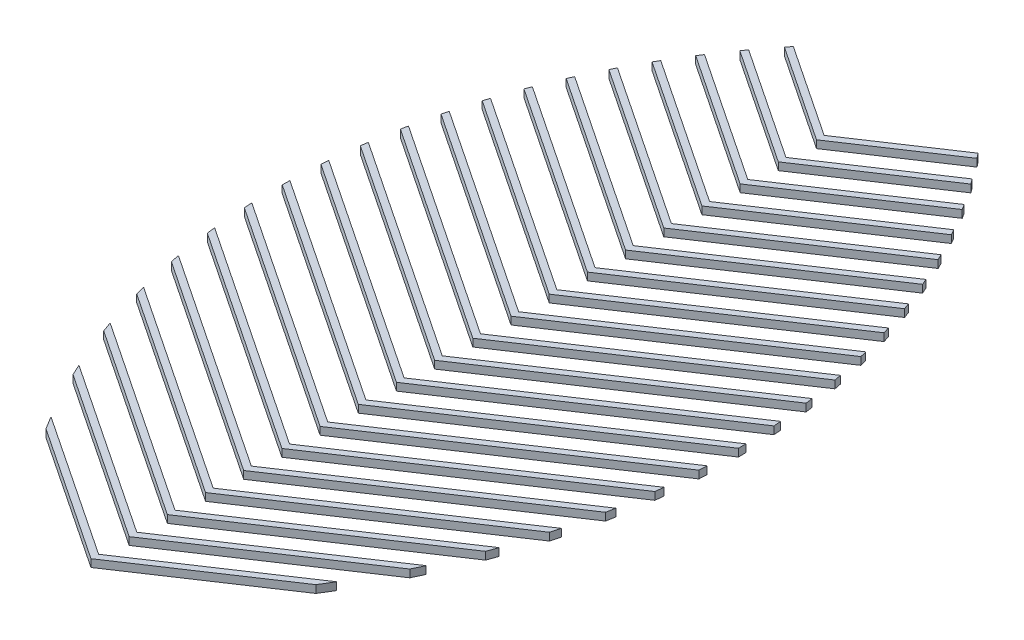
SolidWorks part; units mm, degrees
ref_plane "Front Plane" through (0, 0, 0) normal (0, 0, 1) x (1, 0, 0)
ref_plane "Top Plane" through (0, 0, 0) normal (0, 1, 0) x (1, 0, 0)
ref_plane "Right Plane" through (0, 0, 0) normal (1, 0, 0) x (0, 0, -1)
sketch "Sketch2" plane through (0, 0, 0) normal (0, 1, 0) x (1, 0, 0)
  line L0 (-15.0876, 6.8922) -> (8.6636, -8.942)
  line L1 (8.6636, -8.942) -> (32.4148, 6.8922)
  line L2 (-20.2008, 16.651) -> (8.6636, -2.592)
  line L3 (8.6636, -3.862) -> (8.6636, -8.942) construction
  line L4 (-13.7712, 4.7445) -> (8.6636, -10.212)
  line L5 (8.6636, -10.212) -> (31.0984, 4.7445)
  line L7 (8.6636, -8.942) -> (8.6636, -10.212) construction
  line L9 (8.6636, -2.592) -> (37.5281, 16.651)
  line L10 (-19.336, 14.8045) -> (8.6636, -3.862)
  line L11 (8.6636, -3.862) -> (36.6632, 14.8045)
  line L14 (8.6636, 2.488) -> (8.6636, -2.592) construction
  line L15 (8.6636, -2.592) -> (8.6636, -3.862) construction
  line L16 (-23.6775, 25.3188) -> (8.6636, 3.758)
  line L17 (8.6636, 3.758) -> (41.0047, 25.3188)
  line L18 (-23.0802, 23.6506) -> (8.6636, 2.488)
  line L19 (8.6636, 2.488) -> (40.4074, 23.6506)
  line L22 (8.6636, 8.838) -> (8.6636, 3.758) construction
  line L23 (8.6636, 3.758) -> (8.6636, 2.488) construction
  line L24 (-26.0837, 33.2729) -> (8.6636, 10.108)
  line L25 (8.6636, 10.108) -> (43.4109, 33.2729)
  line L26 (-25.6722, 31.7286) -> (8.6636, 8.838)
  line L27 (8.6636, 8.838) -> (42.9994, 31.7286)
  line L30 (8.6636, 15.188) -> (8.6636, 10.108) construction
  line L31 (8.6636, 10.108) -> (8.6636, 8.838) construction
  line L32 (-27.7036, 40.7028) -> (8.6636, 16.458)
  line L33 (8.6636, 16.458) -> (45.0308, 40.7028)
  line L34 (-27.4334, 39.2527) -> (8.6636, 15.188)
  line L35 (8.6636, 15.188) -> (44.7606, 39.2527)
  line L38 (8.6636, 21.538) -> (8.6636, 16.458) construction
  line L39 (8.6636, 16.458) -> (8.6636, 15.188) construction
  line L40 (-28.7043, 47.72) -> (8.6636, 22.808)
  line L41 (8.6636, 22.808) -> (46.0315, 47.72)
  line L42 (-28.5479, 46.3457) -> (8.6636, 21.538)
  line L43 (8.6636, 21.538) -> (45.8752, 46.3457)
  line L46 (8.6636, 27.888) -> (8.6636, 22.808) construction
  line L47 (8.6636, 22.808) -> (8.6636, 21.538) construction
  line L48 (-29.1937, 54.3963) -> (8.6636, 29.158)
  line L49 (8.6636, 29.158) -> (46.5209, 54.3963)
  line L50 (-29.1328, 53.0857) -> (8.6636, 27.888)
  line L51 (8.6636, 27.888) -> (46.4601, 53.0857)
  line L54 (8.6636, 34.238) -> (8.6636, 29.158) construction
  line L55 (8.6636, 29.158) -> (8.6636, 27.888) construction
  line L56 (-29.246, 60.7811) -> (8.6636, 35.508)
  line L57 (8.6636, 35.508) -> (46.5732, 60.7811)
  line L58 (-29.2677, 59.5256) -> (8.6636, 34.238)
  line L59 (8.6636, 34.238) -> (46.5949, 59.5256)
  line L62 (8.6636, 40.588) -> (8.6636, 35.508) construction
  line L63 (8.6636, 35.508) -> (8.6636, 34.238) construction
  line L64 (-28.9145, 66.9101) -> (8.6636, 41.858)
  line L65 (8.6636, 41.858) -> (46.2417, 66.9101)
  line L66 (-29.0094, 65.7034) -> (8.6636, 40.588)
  line L67 (8.6636, 40.588) -> (46.3367, 65.7034)
  line L70 (8.6636, 46.938) -> (8.6636, 41.858) construction
  line L71 (8.6636, 41.858) -> (8.6636, 40.588) construction
  line L72 (-28.2388, 72.8096) -> (8.6636, 48.208)
  line L73 (8.6636, 48.208) -> (45.566, 72.8096)
  line L74 (-28.3999, 71.647) -> (8.6636, 46.938)
  line L75 (8.6636, 46.938) -> (45.7271, 71.647)
  line L78 (8.6636, 53.288) -> (8.6636, 48.208) construction
  line L79 (8.6636, 48.208) -> (8.6636, 46.938) construction
  line L80 (-27.2489, 78.4997) -> (8.6636, 54.558)
  line L81 (8.6636, 54.558) -> (44.5761, 78.4997)
  line L82 (-27.4708, 77.3777) -> (8.6636, 53.288)
  line L83 (8.6636, 53.288) -> (44.798, 77.3777)
  line L86 (8.6636, 59.638) -> (8.6636, 54.558) construction
  line L87 (8.6636, 54.558) -> (8.6636, 53.288) construction
  line L88 (-25.968, 83.9958) -> (8.6636, 60.908)
  line L89 (8.6636, 60.908) -> (43.2952, 83.9958)
  line L90 (-26.2465, 82.9115) -> (8.6636, 59.638)
  line L91 (8.6636, 59.638) -> (43.5737, 82.9115)
  line L94 (8.6636, 65.988) -> (8.6636, 60.908) construction
  line L95 (8.6636, 60.908) -> (8.6636, 59.638) construction
  line L96 (-24.4139, 89.3097) -> (8.6636, 67.258)
  line L97 (8.6636, 67.258) -> (41.7411, 89.3097)
  line L98 (-24.7458, 88.261) -> (8.6636, 65.988)
  line L99 (8.6636, 65.988) -> (42.073, 88.261)
  line L102 (8.6636, 72.338) -> (8.6636, 67.258) construction
  line L103 (8.6636, 67.258) -> (8.6636, 65.988) construction
  line L104 (-22.6004, 94.4507) -> (8.6636, 73.608)
  line L105 (8.6636, 73.608) -> (39.9276, 94.4507)
  line L106 (-22.9833, 93.436) -> (8.6636, 72.338)
  line L107 (8.6636, 72.338) -> (40.3105, 93.436)
  line L110 (8.6636, 78.688) -> (8.6636, 73.608) construction
  line L111 (8.6636, 73.608) -> (8.6636, 72.338) construction
  line L112 (-20.5381, 99.4258) -> (8.6636, 79.958)
  line L113 (8.6636, 79.958) -> (37.8653, 99.4258)
  line L114 (-20.9701, 98.4438) -> (8.6636, 78.688)
  line L115 (8.6636, 78.688) -> (38.2973, 98.4438)
  line L118 (8.6636, 85.038) -> (8.6636, 79.958) construction
  line L119 (8.6636, 79.958) -> (8.6636, 78.688) construction
  line L120 (-18.2347, 104.2403) -> (8.6636, 86.308)
  line L121 (8.6636, 86.308) -> (35.562, 104.2403)
  line L122 (-18.7144, 103.29) -> (8.6636, 85.038)
  line L123 (8.6636, 85.038) -> (36.0416, 103.29)
  line L126 (8.6636, 91.388) -> (8.6636, 86.308) construction
  line L127 (8.6636, 86.308) -> (8.6636, 85.038) construction
  line L128 (-15.6958, 108.8976) -> (8.6636, 92.658)
  line L129 (8.6636, 92.658) -> (33.023, 108.8976)
  line L130 (-16.2222, 107.9786) -> (8.6636, 91.388)
  line L131 (8.6636, 91.388) -> (33.5494, 107.9786)
  line L134 (8.6636, 97.738) -> (8.6636, 92.658) construction
  line L135 (8.6636, 92.658) -> (8.6636, 91.388) construction
  line L136 (-12.9245, 113.4001) -> (8.6636, 99.008)
  line L137 (8.6636, 99.008) -> (30.2517, 113.4001)
  line L138 (-13.4973, 112.512) -> (8.6636, 97.738)
  line L139 (8.6636, 97.738) -> (30.8245, 112.512)
  line L142 (8.6636, 104.088) -> (8.6636, 99.008) construction
  line L143 (8.6636, 99.008) -> (8.6636, 97.738) construction
  line L144 (-9.9223, 117.7486) -> (8.6636, 105.358)
  line L145 (8.6636, 105.358) -> (27.2495, 117.7486)
  line L146 (-10.5412, 116.8912) -> (8.6636, 104.088)
  line L147 (8.6636, 104.088) -> (27.8684, 116.8912)
  line L150 (8.6636, 110.438) -> (8.6636, 105.358) construction
  line L151 (8.6636, 105.358) -> (8.6636, 104.088) construction
  line L152 (-6.6885, 121.9428) -> (8.6636, 111.708)
  line L153 (8.6636, 111.708) -> (24.0157, 121.9428)
  line L154 (-7.3538, 121.1163) -> (8.6636, 110.438)
  line L155 (8.6636, 110.438) -> (24.6811, 121.1163)
  line L158 (8.6636, 116.788) -> (8.6636, 111.708) construction
  line L159 (8.6636, 111.708) -> (8.6636, 110.438) construction
  arc A0 (-6.6885, 121.9428) -> (-7.3538, 121.1163) centre (71.3713, 58.4122) ccw
  arc A1 (24.0157, 121.9428) -> (24.6811, 121.1163) centre (-54.0441, 58.4122) cw
  arc A2 (32.4148, 6.8922) -> (31.0984, 4.7445) centre (-54.0441, 58.4122) cw
  arc A3 (37.5281, 16.651) -> (36.6632, 14.8045) centre (-54.0441, 58.4122) cw
  arc A4 (41.0047, 25.3188) -> (40.4074, 23.6506) centre (-54.0441, 58.4122) cw
  arc A5 (43.4109, 33.2729) -> (42.9994, 31.7286) centre (-54.0441, 58.4122) cw
  arc A6 (45.0308, 40.7028) -> (44.7606, 39.2527) centre (-54.0441, 58.4122) cw
  arc A7 (46.0315, 47.72) -> (45.8752, 46.3457) centre (-54.0441, 58.4122) cw
  arc A8 (46.5209, 54.3963) -> (46.4601, 53.0857) centre (-54.0441, 58.4122) cw
  arc A9 (46.5732, 60.7811) -> (46.5949, 59.5256) centre (-54.0441, 58.4122) cw
  arc A10 (46.2417, 66.9101) -> (46.3367, 65.7034) centre (-54.0441, 58.4122) cw
  arc A11 (45.566, 72.8096) -> (45.7271, 71.647) centre (-54.0441, 58.4122) cw
  arc A12 (44.5761, 78.4997) -> (44.798, 77.3777) centre (-54.0441, 58.4122) cw
  arc A13 (43.2952, 83.9958) -> (43.5737, 82.9115) centre (-54.0441, 58.4122) cw
  arc A14 (41.7411, 89.3097) -> (42.073, 88.261) centre (-54.0441, 58.4122) cw
  arc A15 (39.9276, 94.4507) -> (40.3105, 93.436) centre (-54.0441, 58.4122) cw
  arc A16 (37.8653, 99.4258) -> (38.2973, 98.4438) centre (-54.0441, 58.4122) cw
  arc A17 (35.562, 104.2403) -> (36.0416, 103.29) centre (-54.0441, 58.4122) cw
  arc A18 (33.023, 108.8976) -> (33.5494, 107.9786) centre (-54.0441, 58.4122) cw
  arc A19 (30.2517, 113.4001) -> (30.8245, 112.512) centre (-54.0441, 58.4122) cw
  arc A20 (27.2495, 117.7486) -> (27.8684, 116.8912) centre (-54.0441, 58.4122) cw
  arc A21 (-15.0876, 6.8922) -> (-13.7712, 4.7445) centre (71.3713, 58.4122) ccw
  arc A22 (-23.6775, 25.3188) -> (-23.0802, 23.6506) centre (71.3713, 58.4122) ccw
  arc A23 (-20.2008, 16.651) -> (-19.336, 14.8045) centre (71.3713, 58.4122) ccw
  arc A24 (-26.0837, 33.2729) -> (-25.6722, 31.7286) centre (71.3713, 58.4122) ccw
  arc A25 (-27.7036, 40.7028) -> (-27.4334, 39.2527) centre (71.3713, 58.4122) ccw
  arc A26 (-28.7043, 47.72) -> (-28.5479, 46.3457) centre (71.3713, 58.4122) ccw
  arc A27 (-29.1937, 54.3963) -> (-29.1328, 53.0857) centre (71.3713, 58.4122) ccw
  arc A28 (-29.246, 60.7811) -> (-29.2677, 59.5256) centre (71.3713, 58.4122) ccw
  arc A29 (-28.9145, 66.9101) -> (-29.0094, 65.7034) centre (71.3713, 58.4122) ccw
  arc A30 (-28.2388, 72.8096) -> (-28.3999, 71.647) centre (71.3713, 58.4122) ccw
  arc A31 (-27.2489, 78.4997) -> (-27.4708, 77.3777) centre (71.3713, 58.4122) ccw
  arc A32 (-25.968, 83.9958) -> (-26.2465, 82.9115) centre (71.3713, 58.4122) ccw
  arc A33 (-24.4139, 89.3097) -> (-24.7458, 88.261) centre (71.3713, 58.4122) ccw
  arc A34 (-22.6004, 94.4507) -> (-22.9833, 93.436) centre (71.3713, 58.4122) ccw
  arc A35 (-20.5381, 99.4258) -> (-20.9701, 98.4438) centre (71.3713, 58.4122) ccw
  arc A36 (-18.2347, 104.2403) -> (-18.7144, 103.29) centre (71.3713, 58.4122) ccw
  arc A37 (-15.6958, 108.8976) -> (-16.2222, 107.9786) centre (71.3713, 58.4122) ccw
  arc A38 (-12.9245, 113.4001) -> (-13.4973, 112.512) centre (71.3713, 58.4122) ccw
  arc A39 (-9.9223, 117.7486) -> (-10.5412, 116.8912) centre (71.3713, 58.4122) ccw
  point P0 (0, 0)
  dimension "D1" = 1.27
  dimension "D3" = 20
extrude "Boss-Extrude1" add sketch "Sketch2" along normal blind 1.27
scale "Scale2" bodies to scale 104 117 109 101 114 106 119 111 103 116 108 113 105 118 110 102 115 107 120 112 scale about origin uniform scaling yes scale factor 2
